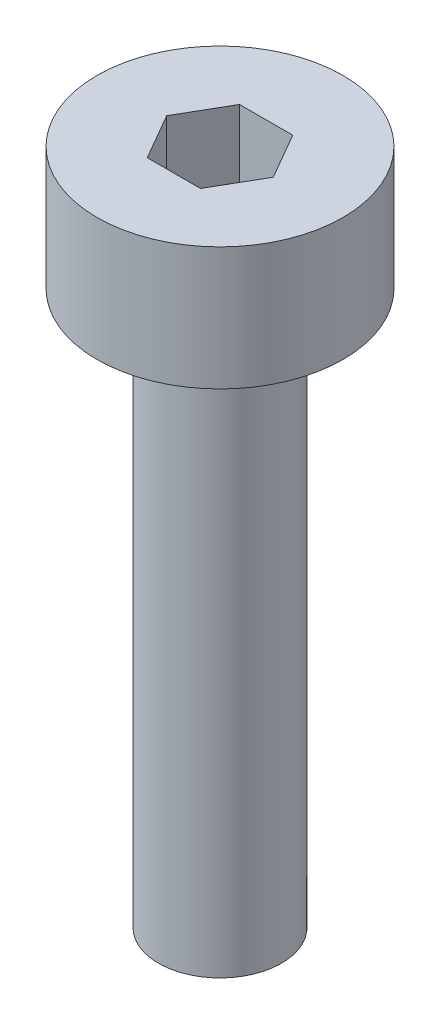
SolidWorks part; units mm, degrees
material "AISI 304"
ref_plane "前视基准面" through (0, 0, 0) normal (0, 0, 1) x (1, 0, 0)
ref_plane "上视基准面" through (0, 0, 0) normal (0, 1, 0) x (1, 0, 0)
ref_plane "右视基准面" through (0, 0, 0) normal (1, 0, 0) x (0, 0, -1)
sketch "草图1" plane through (0, 0, 0) normal (0, 1, 0) x (1, 0, 0)
  circle A0 centre (0, 0) radius 2
  dimension "D1" = 4
extrude "杯头高度" add sketch "草图1" along normal blind 2
sketch "草图2" plane through (0, 2, 0) normal (0, 1, 0) x (1, 0, 0)
  line L1 (0.866, 0) -> (0.433, 0.75)
  line L2 (0.433, 0.75) -> (-0.433, 0.75)
  line L3 (-0.433, 0.75) -> (-0.866, 0)
  line L4 (-0.866, 0) -> (-0.433, -0.75)
  line L5 (-0.433, -0.75) -> (0.433, -0.75)
  line L6 (0.433, -0.75) -> (0.866, 0)
  circle A0 centre (0, 0) radius 0.75 construction
  dimension "D1" = 1.5
extrude "内六角深度" cut sketch "草图2" against normal blind 1.5
sketch "草图3" plane through (0, 0, 0) normal (0, -1, 0) x (1, 0, 0)
  circle A0 centre (0, 0) radius 1
  dimension "D1" = 2
extrude "螺纹长度" add sketch "草图3" along normal blind 9
